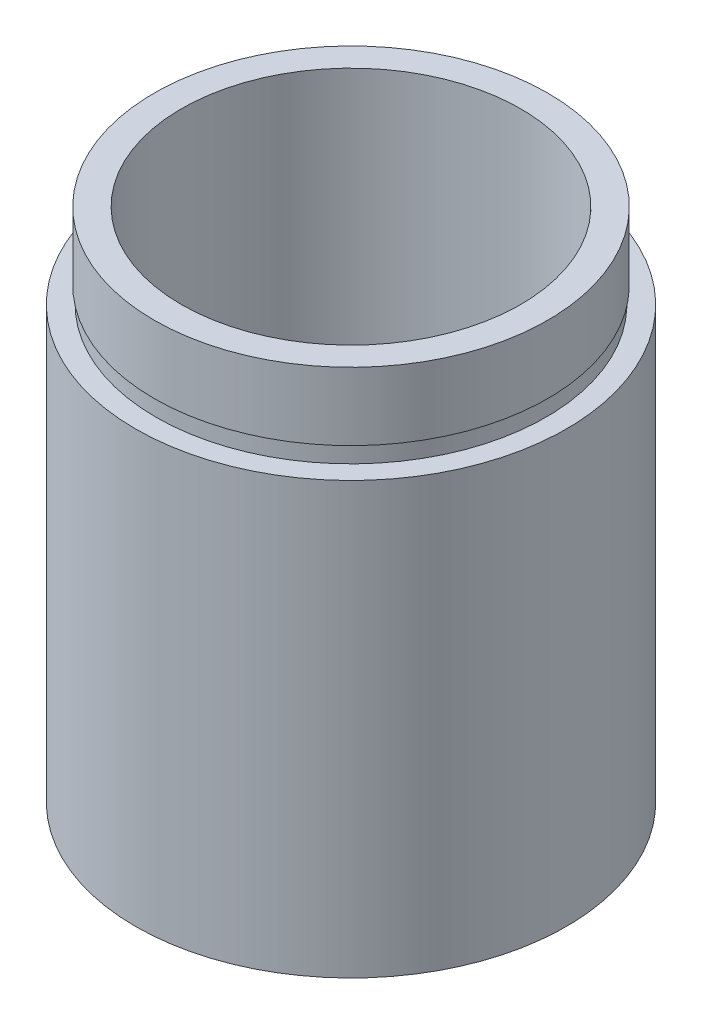
SolidWorks part; units mm, degrees
ref_plane "前视基准面" through (0, 0, 0) normal (0, 0, 1) x (1, 0, 0)
ref_plane "上视基准面" through (0, 0, 0) normal (0, 1, 0) x (1, 0, 0)
ref_plane "右视基准面" through (0, 0, 0) normal (1, 0, 0) x (0, 0, -1)
sketch "草图1" plane through (0, 0, 0) normal (0, 0, 1) x (1, 0, 0)
  line L0 (0, 161.3762) -> (0, 0) construction
  line L1 (141.7365, 0) -> (-131.7984, 0) construction
  line L2 (12.7, 0) -> (12.7, 25.4)
  line L3 (11.1, 4.5) -> (11.7, 4.5)
  line L4 (11.1, 0) -> (12.7, 0)
  line L5 (11.7, 4.5) -> (11.7, 5.5)
  line L6 (10, 5.5) -> (10, 30.4)
  line L7 (11.1, 4.5) -> (11.1, 0)
  line L8 (11.7, 5.5) -> (10, 5.5)
  line L9 (11.5, 26.4) -> (11.5, 25.4)
  line L10 (12.7, 25.4) -> (11.5, 25.4)
  line L11 (11.6, 26.4) -> (11.6, 30.4)
  line L12 (11.5, 26.4) -> (11.6, 26.4)
  line L13 (11.6, 30.4) -> (10, 30.4)
  dimension "D2" = 12.7
  dimension "D3" = 11.7
  dimension "D4" = 10
  dimension "D5" = 11.5
  dimension "D6" = 11.6
  dimension "D7" = 1
  dimension "D8" = 25.4
  dimension "D9" = 5
  dimension "D10" = 1
  dimension "D11" = 11.1
  dimension "D12" = 4.5
revolve "旋转1" add sketch "草图1" angle 360 about L0
cosmetic thread "装饰螺纹线1" parameters "D2"=23.2
cosmetic thread "装饰螺纹线2" parameters "D2"=21
cosmetic thread "装饰螺纹线3" parameters "D2"=23
